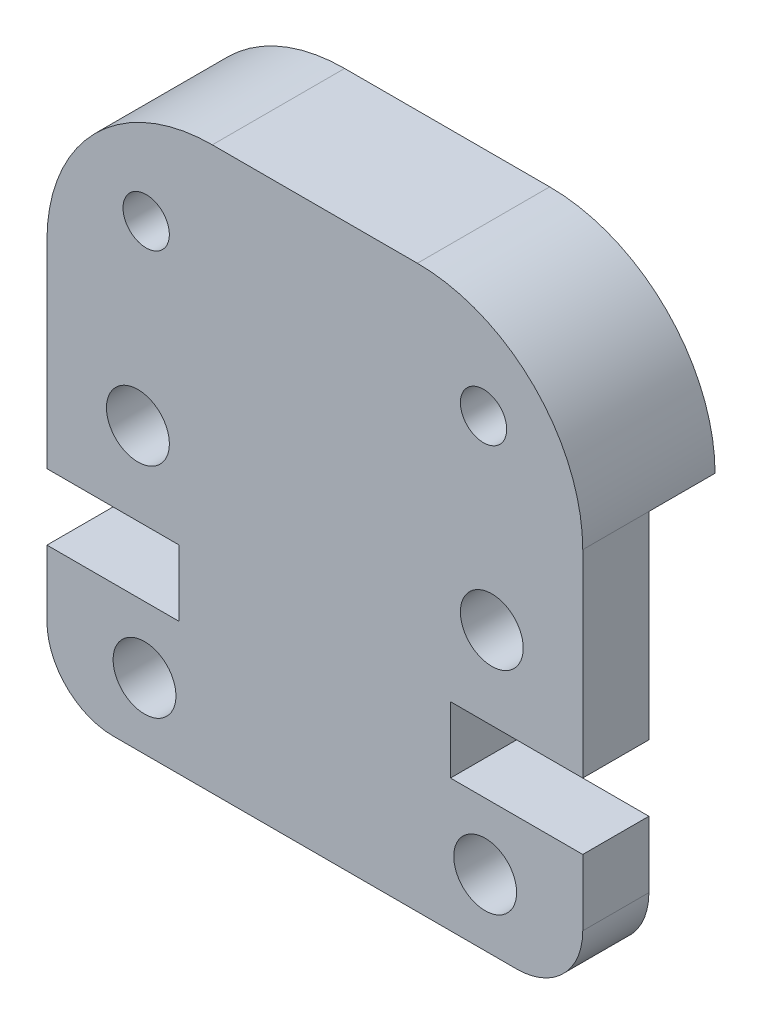
SolidWorks part; units mm, degrees
ref_plane "Front Plane" through (0, 0, 0) normal (0, 0, 1) x (1, 0, 0)
ref_plane "Top Plane" through (0, 0, 0) normal (0, 1, 0) x (1, 0, 0)
ref_plane "Right Plane" through (0, 0, 0) normal (1, 0, 0) x (0, 0, -1)
sketch "Sketch1" plane through (0, 0, 0) normal (0, 0, 1) x (1, 0, 0)
  line L0 (0, 16.98) -> (0, 0) construction
  line L1 (3.1, 16.98) -> (-3.1, 16.98)
  line L2 (6.1, 0) -> (-6.1, 0)
  line L3 (-8.1, 6) -> (-4.1, 6)
  line L4 (-4.1, 6) -> (-4.1, 4)
  line L5 (-4.1, 4) -> (-8.1, 4)
  line L6 (-8.1, 2) -> (-8.1, 4)
  line L7 (8.1, 11.98) -> (8.1, 6)
  line L8 (-8.1, 11.98) -> (-8.1, 6)
  line L9 (5.1, 13.98) -> (0, 13.98) construction
  line L24 (8.1, 2) -> (8.1, 4)
  line L27 (4.1, 4) -> (8.1, 4)
  line L30 (4.1, 6) -> (4.1, 4)
  line L31 (8.1, 6) -> (4.1, 6)
  circle A0 centre (-5.15, 2) radius 0.95
  circle A1 centre (-5.1, 13.98) radius 0.7
  arc A2 (-8.1, 11.98) -> (-3.1, 16.98) centre (-3.1, 11.98) cw
  arc A3 (-6.1, 0) -> (-8.1, 2) centre (-6.1, 2) cw
  circle A4 centre (-5.35, 8.5) radius 0.95
  circle A5 centre (0, 13.98) radius 0.7 construction
  circle A10 centre (5.35, 8.5) radius 0.95
  arc A12 (6.1, 0) -> (8.1, 2) centre (6.1, 2) ccw
  arc A14 (8.1, 11.98) -> (3.1, 16.98) centre (3.1, 11.98) ccw
  circle A16 centre (5.1, 13.98) radius 0.7
  circle A18 centre (5.15, 2) radius 0.95
  dimension "D1" = 1.9
  dimension "D2" = 1.4
  dimension "D3" = 16.98
  dimension "D4" = 2
  dimension "D5" = 5
  dimension "D6" = 6.1
  dimension "D7" = 3
  dimension "D8" = 3
  dimension "D9" = 2.75
  dimension "D10" = 8.5
extrude "Boss-Extrude1" add sketch "Sketch1" along normal blind 4
sketch "Sketch2" plane through (0, 0, 0) normal (0, 0, 1) x (1, 0, 0)
  line L0 (-8.1, 0) -> (8.1, 0)
  line L1 (8.1, 0) -> (8.1, 11.98)
  line L2 (8.1, 11.98) -> (-8.1, 11.98)
  line L3 (-8.1, 11.98) -> (-8.1, 0)
extrude "Cut-Extrude1" cut sketch "Sketch2" along normal blind 2
